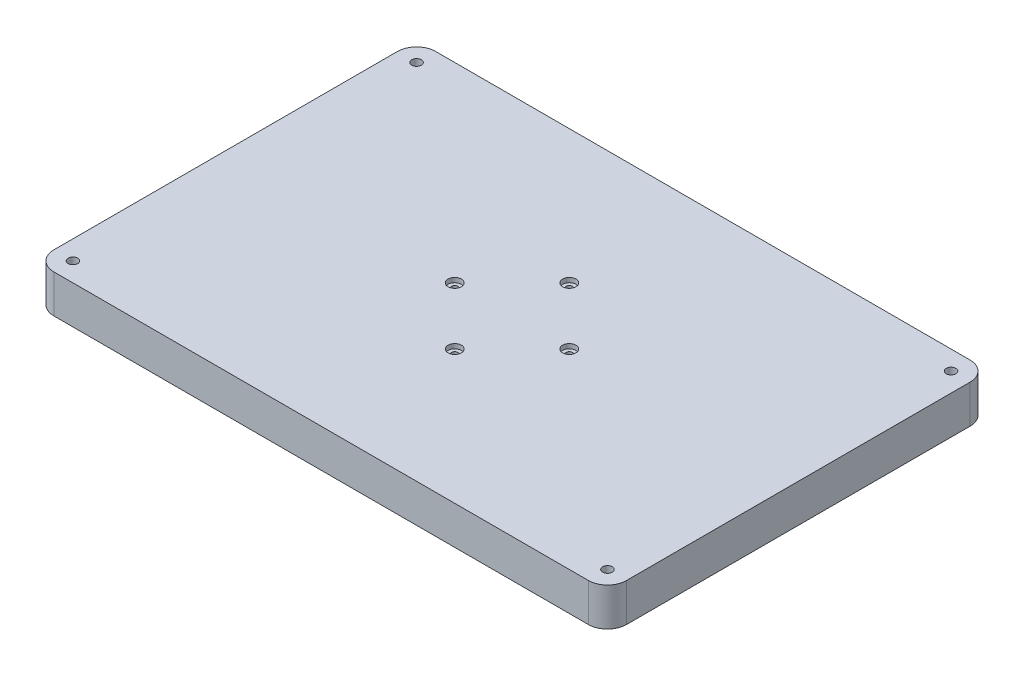
SolidWorks part; units mm, degrees
ref_plane "Front Plane" through (0, 0, 0) normal (0, 0, 1) x (1, 0, 0)
ref_plane "Top Plane" through (0, 0, 0) normal (0, 1, 0) x (1, 0, 0)
ref_plane "Right Plane" through (0, 0, 0) normal (1, 0, 0) x (0, 0, -1)
sketch "Sketch1" plane through (0, 0, 0) normal (0, 1, 0) x (1, 0, 0)
  line L1 (150, 100) -> (-150, 100)
  line L2 (150, 100) -> (150, -100)
  line L3 (150, -100) -> (-150, -100)
  line L4 (-150, 100) -> (-150, -100)
  line L5 (150, 100) -> (-150, -100) construction
  line L6 (150, -100) -> (-150, 100) construction
  point P0 (0, 0)
  dimension "D1" = 200
  dimension "D2" = 300
extrude "Boss-Extrude1" add sketch "Sketch1" along normal blind 20
fillet "Fillet1" radius 10 4 edges at (-150, 10, -100) (-150, 10, 100) (150, 10, 100) (150, 10, -100)
hole_wizard "CBORE for M3 Pan Head Machine Screw1" positions "Sketch4" profile "Sketch3" counterbore size "M3" standard "ANSI Metric" end condition through all
sketch "Sketch4" plane through (0, 20, 0) normal (0, 1, 0) x (1, 0, 0)
  circle A0 centre (0, 0) radius 40
  circle A1 centre (0, 0) radius 30
  point P0 (-30, 0)
  point P2 (0, -30)
  point P4 (30, 0)
  point P6 (0, 30)
sketch "Sketch3" plane through (-30, 20, 0) normal (1, 0, 0) x (0, 0, 1)
  line L0 (0, 0) -> (0, 20)
  line L1 (0, 20) -> (1.7, 20)
  line L3 (1.7, 20) -> (1.7, 2.4)
  line L4 (1.7, 2.4) -> (3.5, 2.4)
  line L5 (3.5, 2.4) -> (3.5, 0)
  line L7 (3.5, 0) -> (0, 0)
  line L11 (0, -6.35) -> (0, 107.95) construction
  dimension "Thru Hole Dia." = 3.4
  dimension "Thru Hole Depth" = 20
  dimension "C'Bore Dia." = 7
  dimension "C'Bore Depth" = 2.4
hole_wizard "Ø5.0 (5) Diameter Hole1" positions "Sketch7" profile "Sketch5" hole size "Ø5.0" standard "ANSI Metric" end condition through all
sketch "Sketch7" plane through (0, 20, 0) normal (0, 1, 0) x (1, 0, 0)
  point P0 (-140, 90)
  point P2 (140, 90)
  point P4 (140, -90)
  point P6 (-140, -90)
sketch "Sketch5" plane through (-140, 20, -90) normal (1, 0, 0) x (0, 0, 1)
  line L0 (0, 0) -> (0, 20)
  line L1 (0, 20) -> (2.5, 20)
  line L2 (2.5, 20) -> (2.5, 0)
  line L5 (2.5, 0) -> (0, 0)
  line L11 (0, -6.35) -> (0, 107.95) construction
  dimension "Thru Hole Dia." = 5
  dimension "Thru Hole Depth" = 20
hole_wizard "Ø2.0 (2) Diameter Hole1" positions "Sketch10" profile "Sketch8" hole size "Ø2.0" standard "ANSI Metric"
sketch "Sketch10" plane through (0, 0, 0) normal (0, -1, 0) x (-1, 0, 0)
  point P0 (129.0085, -60.2814)
  point P10 (123.8897, -7.8832)
  point P13 (95.9897, -7.8932)
  point P23 (80.7079, -58.6987)
sketch "Sketch8" plane through (-129.0085, 0, 60.2814) normal (1, 0, 0) x (0, 0, -1)
  line L0 (0, 0) -> (0, 10.6009)
  line L1 (0, 10.6009) -> (1, 10)
  line L2 (1, 10) -> (1, 0)
  line L5 (1, 0) -> (0, 0)
  line L10 (0, 10.6009) -> (-1, 10) construction
  line L11 (0, -6.35) -> (0, 107.95) construction
  dimension "Hole Dia." = 2
  dimension "Hole Depth" = 10
  dimension "Drill Angle" = 118
